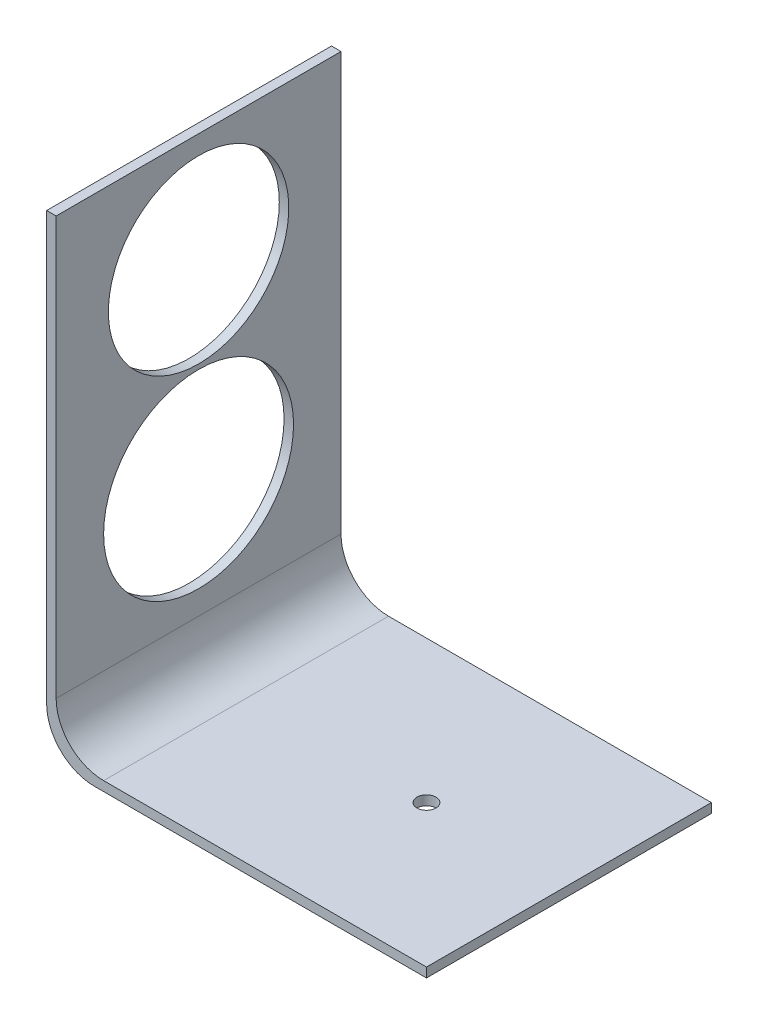
SolidWorks part; units mm, degrees
ref_plane "Front Plane" through (0, 0, 0) normal (0, 0, 1) x (1, 0, 0)
ref_plane "Top Plane" through (0, 0, 0) normal (0, 1, 0) x (1, 0, 0)
ref_plane "Right Plane" through (0, 0, 0) normal (1, 0, 0) x (0, 0, -1)
sketch "Sketch1" plane through (0, 0, 0) normal (0, 0, 1) x (1, 0, 0)
  line L0 (-24.8276, 75.2586) -> (-22.8276, 75.2586)
  line L1 (-22.8276, 75.2586) -> (-22.8276, -12.7414)
  line L2 (-12.8276, -22.7414) -> (55.1724, -22.7414)
  line L3 (55.1724, -22.7414) -> (55.1724, -24.7414)
  line L4 (55.1724, -24.7414) -> (-14.8276, -24.7414)
  line L5 (-24.8276, -14.7414) -> (-24.8276, 75.2586)
  arc A0 (-14.8276, -24.7414) -> (-24.8276, -14.7414) centre (-14.8276, -14.7414) cw
  arc A1 (-12.8276, -22.7414) -> (-22.8276, -12.7414) centre (-12.8276, -12.7414) cw
  point P8 (-24.8276, -24.7414)
  dimension "D5" = 10
  dimension "D1" = 100
  dimension "D2" = 80
  dimension "D3" = 2
  dimension "D4" = 2
extrude "Boss-Extrude1" add sketch "Sketch1" along normal blind 60
sketch "Sketch2" plane through (-22.8276, 0, 0) normal (1, 0, 0) x (0, 0, -1)
  line L0 (-60, -12.7414) -> (0, -12.7414) construction
  circle A0 centre (-30, 12.2586) radius 20
  circle A1 centre (-30, 52.2586) radius 19
  point P6 (-30, -12.7414)
  dimension "D1" = 40
  dimension "D3" = 38
  dimension "D2" = 40
  dimension "D4" = 25
extrude "Cut-Extrude1" cut sketch "Sketch2" against normal blind 10 contours A0 | A1
sketch "Sketch3" plane through (0, -22.7414, 0) normal (0, 1, 0) x (1, 0, 0)
  line L0 (55.1724, -60) -> (55.1724, 0) construction
  circle A0 centre (25.1724, -30) radius 2
  point P4 (55.1724, -30)
  dimension "D1" = 4
  dimension "D2" = 30
extrude "Cut-Extrude2" cut sketch "Sketch3" against normal blind 10
